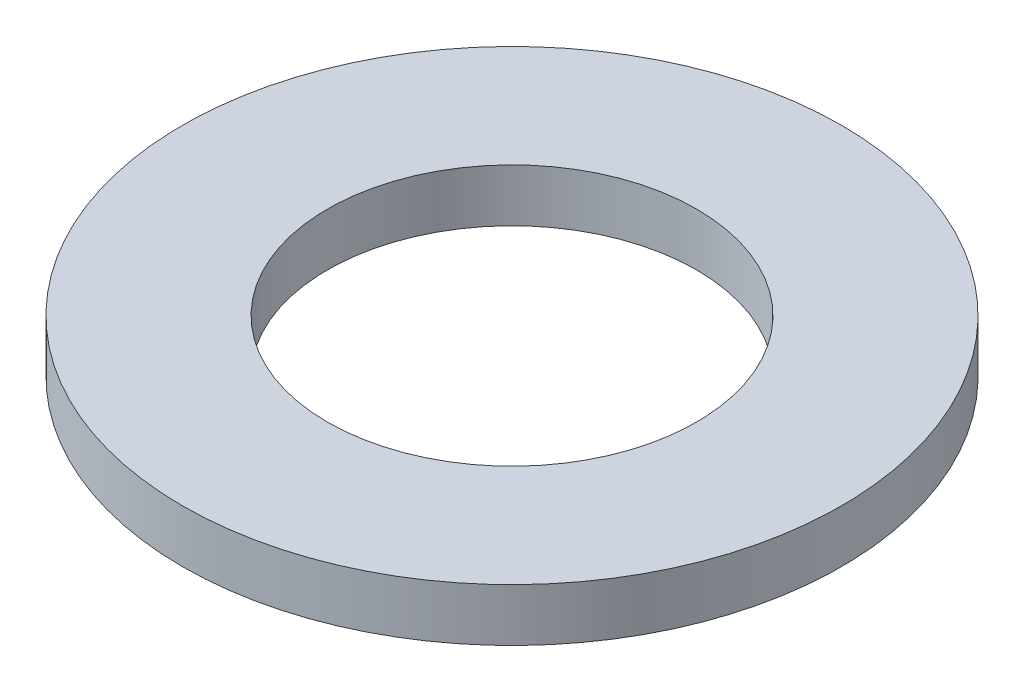
SolidWorks part; units mm, degrees
ref_plane "Front Plane" through (0, 0, 0) normal (0, 0, 1) x (1, 0, 0)
ref_plane "Top Plane" through (0, 0, 0) normal (0, 1, 0) x (1, 0, 0)
ref_plane "Right Plane" through (0, 0, 0) normal (1, 0, 0) x (0, 0, -1)
sketch "Sketch1" plane through (0, 0, 0) normal (0, 1, 0) x (1, 0, 0)
  circle A0 centre (0, 0) radius 7
  circle A1 centre (0, 0) radius 12.5
extrude "Boss-Extrude1" add sketch "Sketch1" along normal blind 2
